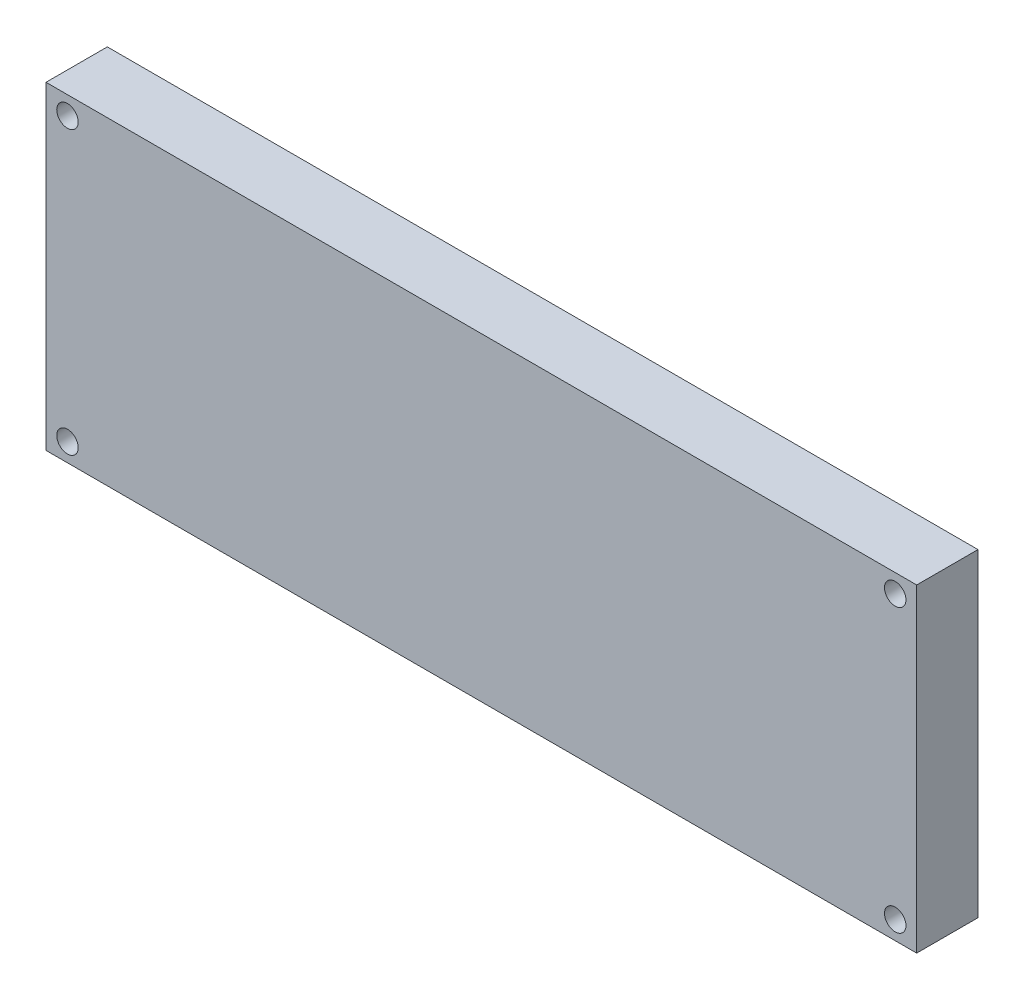
SolidWorks part; units mm, degrees
ref_plane "Front Plane" through (0, 0, 0) normal (0, 0, 1) x (1, 0, 0)
ref_plane "Top Plane" through (0, 0, 0) normal (0, 1, 0) x (1, 0, 0)
ref_plane "Right Plane" through (0, 0, 0) normal (1, 0, 0) x (0, 0, -1)
sketch "Sketch1" plane through (0, 0, 0) normal (0, 0, 1) x (1, 0, 0)
  line L0 (71, 52) -> (71, 37.7097) construction
  line L1 (0, 0) -> (142, 0)
  line L2 (0, 0) -> (0, 52)
  line L3 (0, 52) -> (142, 52)
  line L4 (142, 0) -> (142, 52)
  line L5 (0, 26) -> (43.4792, 26) construction
  circle A0 centre (138.5, 49) radius 1.75
  circle A1 centre (3.5, 49) radius 1.75
  circle A2 centre (3.5, 3) radius 1.75
  circle A3 centre (138.5, 3) radius 1.75
  dimension "D5" = 3.5
  dimension "D1" = 142
  dimension "D2" = 52
  dimension "D3" = 135
  dimension "D4" = 46
extrude "Boss-Extrude1" add sketch "Sketch1" along normal blind 10
